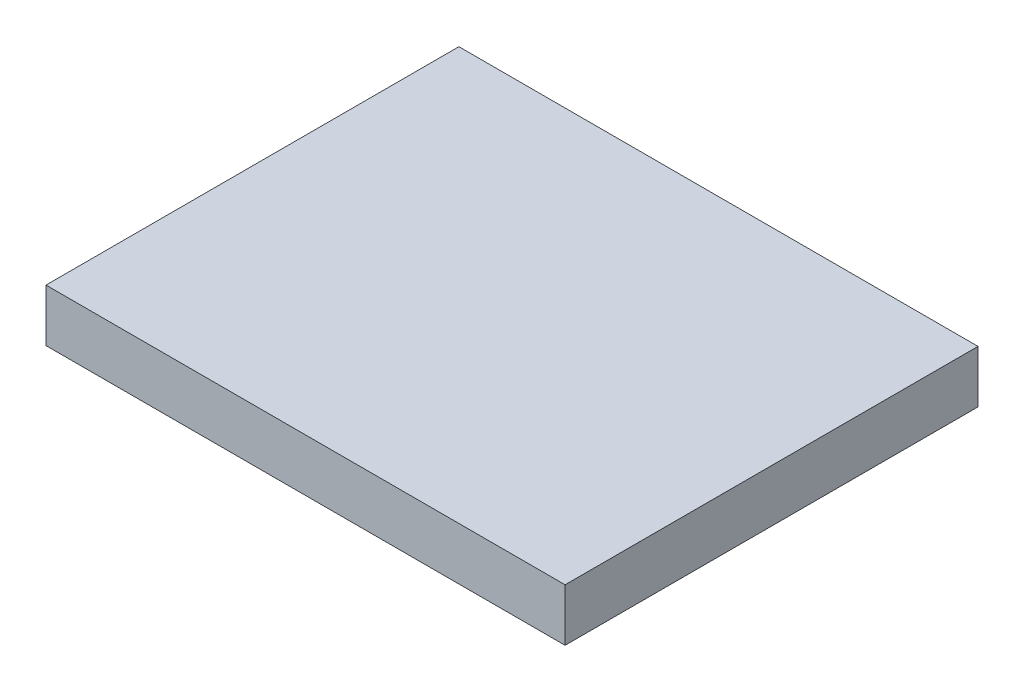
SolidWorks part; units mm, degrees
ref_plane "Front Plane" through (0, 0, 0) normal (0, 0, 1) x (1, 0, 0)
ref_plane "Top Plane" through (0, 0, 0) normal (0, 1, 0) x (1, 0, 0)
ref_plane "Right Plane" through (0, 0, 0) normal (1, 0, 0) x (0, 0, -1)
sketch "Sketch1" plane through (0, 0, 0) normal (0, 1, 0) x (1, 0, 0)
  line L1 (-220, -175) -> (220, -175)
  line L2 (-220, -175) -> (-220, 175)
  line L3 (-220, 175) -> (220, 175)
  line L4 (220, -175) -> (220, 175)
  line L5 (-220, -175) -> (220, 175) construction
  line L6 (-220, 175) -> (220, -175) construction
  point P0 (0, 0)
  dimension "D1" = 440
  dimension "D2" = 350
extrude "Boss-Extrude1" add sketch "Sketch1" along normal blind 44.45
